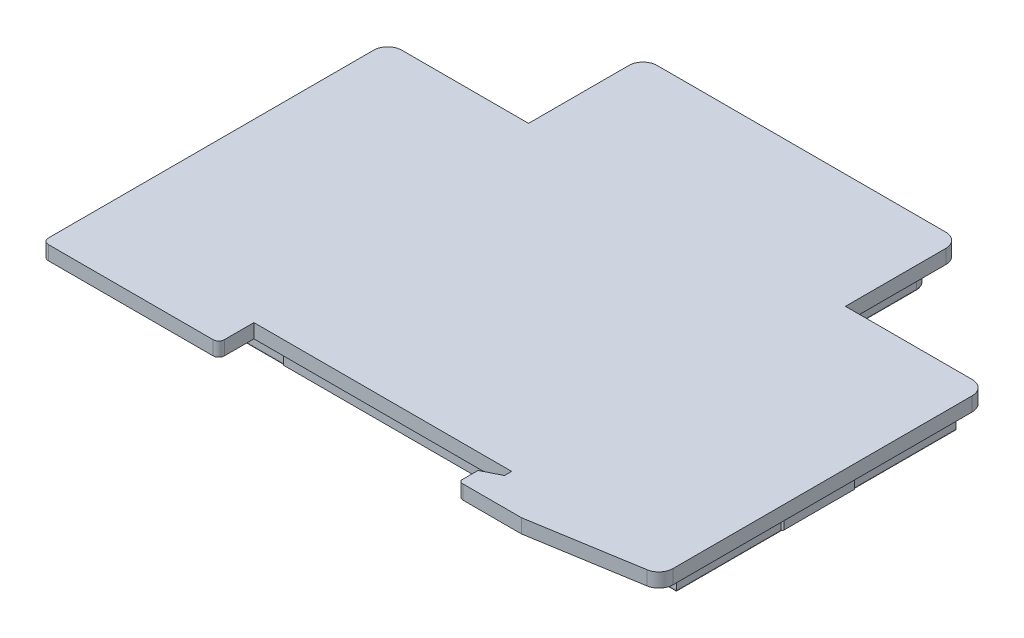
SolidWorks part; units mm, degrees
ref_plane "Front Plane" through (0, 0, 0) normal (0, 0, 1) x (1, 0, 0)
ref_plane "Top Plane" through (0, 0, 0) normal (0, 1, 0) x (1, 0, 0)
ref_plane "Right Plane" through (0, 0, 0) normal (1, 0, 0) x (0, 0, -1)
sketch "Sketch1" plane through (0, 0, 0) normal (0, 1, 0) x (1, 0, 0)
  line L74 (19.5863, 59.9772) -> (19.5863, 47.7272)
  line L75 (58.4363, 61.8272) -> (21.4363, 61.8272)
  line L76 (60.2863, 47.7272) -> (60.2863, 59.9772)
  line L77 (80.2863, 45.5772) -> (62.4363, 45.5772)
  line L78 (80.2863, 5.8772) -> (80.2863, 45.5772)
  line L79 (-0.4137, 5.8772) -> (80.2863, 5.8772)
  line L80 (-0.4137, 45.5772) -> (-0.4137, 5.8772)
  line L81 (17.4363, 45.5772) -> (-0.4137, 45.5772)
  line L82 (19.5863, 59.9772) -> (19.5863, 47.7272)
  line L83 (58.4363, 61.8272) -> (21.4363, 61.8272)
  line L84 (60.2863, 47.7272) -> (60.2863, 59.9772)
  line L85 (80.2863, 45.5772) -> (62.4363, 45.5772)
  line L86 (80.2863, 5.8772) -> (80.2863, 45.5772)
  line L87 (-0.4137, 5.8772) -> (80.2863, 5.8772)
  line L88 (-0.4137, 45.5772) -> (-0.4137, 5.8772)
  line L89 (17.4363, 45.5772) -> (-0.4137, 45.5772)
  arc A20 (17.4363, 45.5772) -> (19.5863, 47.7272) centre (17.4363, 47.7272) ccw
  arc A21 (21.4363, 61.8272) -> (19.5863, 59.9772) centre (21.4363, 59.9772) ccw
  arc A22 (60.2863, 59.9772) -> (58.4363, 61.8272) centre (58.4363, 59.9772) ccw
  arc A23 (60.2863, 47.7272) -> (62.4363, 45.5772) centre (62.4363, 47.7272) ccw
  arc A24 (17.4363, 45.5772) -> (19.5863, 47.7272) centre (17.4363, 47.7272) ccw
  arc A25 (21.4363, 61.8272) -> (19.5863, 59.9772) centre (21.4363, 59.9772) ccw
  arc A26 (60.2863, 59.9772) -> (58.4363, 61.8272) centre (58.4363, 59.9772) ccw
  arc A27 (60.2863, 47.7272) -> (62.4363, 45.5772) centre (62.4363, 47.7272) ccw
  dimension "D1" = 0.15
extrude "Boss-Extrude1" add sketch "Sketch1" along normal blind 3.3
sketch "Sketch2" plane through (0, 3.3, 0) normal (0, 1, 0) x (1, 0, 0)
  line L15 (56.3363, 1.5772) -> (56.3363, -0.4728)
  line L16 (57.1363, -1.2728) -> (65.4363, -1.2728)
  line L17 (65.4363, -1.2728) -> (80.7613, 1.2513)
  line L18 (82.4363, 3.2247) -> (82.4363, 45.7272)
  line L19 (80.4363, 47.7272) -> (76.4363, 47.7272)
  line L20 (62.4363, 47.7272) -> (62.4363, 61.9772)
  line L21 (60.4363, 63.9772) -> (19.4363, 63.9772)
  line L22 (17.4363, 61.9772) -> (17.4363, 47.7272)
  line L23 (17.4363, 47.7272) -> (13.4363, 47.7272)
  line L24 (-2.5637, 45.7272) -> (-2.5637, -0.4728)
  line L25 (-1.7637, -1.2728) -> (21.6363, -1.2728)
  line L26 (22.4363, -0.4728) -> (22.4363, 3.7272)
  line L27 (22.4363, 3.7272) -> (58.8363, 3.7272)
  line L28 (58.8363, 3.7272) -> (58.8363, 2.8272)
  line L29 (58.8363, 2.8272) -> (56.3363, 1.5772)
  line L30 (56.3363, 1.5772) -> (56.3363, -0.4728) construction
  line L31 (57.1363, -1.2728) -> (65.4363, -1.2728)
  line L32 (65.4363, -1.2728) -> (80.7613, 1.2513)
  line L33 (82.4363, 3.2247) -> (82.4363, 45.7272)
  line L34 (80.4363, 47.7272) -> (66.4363, 47.7272)
  line L35 (62.4363, 47.7272) -> (62.4363, 61.9772)
  line L36 (60.4363, 63.9772) -> (19.4363, 63.9772)
  line L37 (17.4363, 61.9772) -> (17.4363, 47.7272)
  line L38 (17.4363, 47.7272) -> (3.4363, 47.7272)
  line L39 (-2.5637, 45.7272) -> (-2.5637, -0.4728)
  line L40 (-1.7637, -1.2728) -> (21.6363, -1.2728)
  line L41 (22.4363, -0.4728) -> (22.4363, 3.7272)
  line L42 (22.4363, 3.7272) -> (59.0363, 3.7272)
  line L43 (58.8363, 3.7272) -> (58.8363, 2.8272) construction
  line L44 (58.8363, 2.8272) -> (56.3363, 1.5772) construction
  line L90 (59.0363, 3.7272) -> (59.0363, 2.7036)
  line L91 (59.0363, 2.7036) -> (56.5363, 1.4536)
  line L92 (56.5363, 1.4536) -> (56.5363, -1.002)
  line L93 (56.5363, 1.4536) -> (56.5363, -0.4728) construction
  line L170 (76.4363, 47.4272) -> (66.4363, 47.4272)
  line L171 (76.4363, 47.4272) -> (66.4363, 47.4272) construction
  line L172 (66.4363, 47.4272) -> (66.4363, 47.7272)
  line L173 (66.4363, 47.4272) -> (66.4363, 47.7272) construction
  line L174 (66.4363, 47.7272) -> (62.4363, 47.7272)
  line L175 (66.4363, 47.7272) -> (62.4363, 47.7272)
  line L176 (13.4363, 47.7272) -> (13.4363, 47.4272)
  line L177 (13.4363, 47.7272) -> (13.4363, 47.4272) construction
  line L178 (13.4363, 47.4272) -> (3.4363, 47.4272)
  line L179 (13.4363, 47.4272) -> (3.4363, 47.4272) construction
  line L180 (3.4363, 47.4272) -> (3.4363, 47.7272)
  line L181 (3.4363, 47.4272) -> (3.4363, 47.7272) construction
  line L182 (3.4363, 47.7272) -> (-0.5637, 47.7272)
  line L183 (3.4363, 47.7272) -> (-0.5637, 47.7272)
  line L184 (76.4363, 47.7272) -> (76.4363, 47.4272)
  line L185 (76.4363, 47.7272) -> (76.4363, 47.4272) construction
  arc A8 (56.3363, -0.4728) -> (57.1363, -1.2728) centre (57.1363, -0.4728) ccw
  arc A9 (80.7613, 1.2513) -> (82.4363, 3.2247) centre (80.4363, 3.2247) ccw
  arc A10 (82.4363, 45.7272) -> (80.4363, 47.7272) centre (80.4363, 45.7272) ccw
  arc A11 (62.4363, 61.9772) -> (60.4363, 63.9772) centre (60.4363, 61.9772) ccw
  arc A12 (19.4363, 63.9772) -> (17.4363, 61.9772) centre (19.4363, 61.9772) ccw
  arc A13 (-0.5637, 47.7272) -> (-2.5637, 45.7272) centre (-0.5637, 45.7272) ccw
  arc A14 (-2.5637, -0.4728) -> (-1.7637, -1.2728) centre (-1.7637, -0.4728) ccw
  arc A15 (21.6363, -1.2728) -> (22.4363, -0.4728) centre (21.6363, -0.4728) ccw
  arc A16 (56.5363, -1.002) -> (57.1363, -1.2728) centre (57.1363, -0.4728) ccw
  arc A17 (80.7613, 1.2513) -> (82.4363, 3.2247) centre (80.4363, 3.2247) ccw
  arc A18 (82.4363, 45.7272) -> (80.4363, 47.7272) centre (80.4363, 45.7272) ccw
  arc A19 (62.4363, 61.9772) -> (60.4363, 63.9772) centre (60.4363, 61.9772) ccw
  arc A20 (19.4363, 63.9772) -> (17.4363, 61.9772) centre (19.4363, 61.9772) ccw
  arc A21 (-0.5637, 47.7272) -> (-2.5637, 45.7272) centre (-0.5637, 45.7272) ccw
  arc A22 (-2.5637, -0.4728) -> (-1.7637, -1.2728) centre (-1.7637, -0.4728) ccw
  arc A23 (21.6363, -1.2728) -> (22.4363, -0.4728) centre (21.6363, -0.4728) ccw
  arc A48 (56.3363, -0.4728) -> (56.5363, -1.002) centre (57.1363, -0.4728) ccw construction
  arc A49 (56.5363, -0.4728) -> (57.1363, -1.0728) centre (57.1363, -0.4728) ccw construction
  arc A50 (56.3363, -0.4728) -> (57.1363, -1.2728) centre (57.1363, -0.4728) ccw construction
  dimension "D1" = 0
  dimension "D2" = 0.2
extrude "Boss-Extrude2" add sketch "Sketch2" along normal blind 2
sketch "Sketch5" plane through (0, 0, -45.5772) normal (0, 0, -1) x (-1, 0, 0)
  line L0 (-80.2863, 3.3) -> (-62.4363, 3.3) construction
  line L1 (-76.4363, 1.8) -> (-66.4363, 1.8)
  line L2 (-76.4363, 1.8) -> (-76.4363, 0.25)
  line L3 (-76.4363, 0.25) -> (-66.4363, 0.25)
  line L4 (-66.4363, 1.8) -> (-66.4363, 0.25)
  line L5 (-80.2863, 0) -> (0.4137, 0) construction
  line L6 (-3.4363, 0.25) -> (-13.4363, 0.25)
  line L7 (-39.9363, -8.663) -> (-39.9363, 0) construction
  line L8 (-13.4363, 1.8) -> (-13.4363, 0.25)
  line L9 (-3.4363, 1.8) -> (-13.4363, 1.8)
  line L10 (-3.4363, 1.8) -> (-3.4363, 0.25)
  line L11 (-76.4363, 1.3) -> (-66.4363, 1.3) construction
  point P16 (-71.4363, 1.8)
  point P19 (-71.4363, 1.3)
  dimension "D1" = 10
  dimension "D2" = 1.5
  dimension "D3" = 1.55
extrude "Boss-Extrude3" add sketch "Sketch5" along normal blind 0.45
sketch "Sketch6" plane through (0, 0, -61.8272) normal (0, 0, -1) x (-1, 0, 0)
  line L1 (-44.9363, 1.8) -> (-34.9363, 1.8)
  line L2 (-44.9363, 1.8) -> (-44.9363, 0.25)
  line L3 (-44.9363, 0.25) -> (-34.9363, 0.25)
  line L4 (-34.9363, 1.8) -> (-34.9363, 0.25)
  line L5 (-58.4363, 0) -> (-21.4363, 0) construction
  line L7 (-58.4363, 3.3) -> (-21.4363, 3.3) construction
  point P6 (-39.9363, 0)
  point P16 (-39.9363, 1.8)
  dimension "D1" = 10
  dimension "D2" = 1.5
  dimension "D3" = 1.55
extrude "Boss-Extrude4" add sketch "Sketch6" along normal blind 0.45
sketch "Sketch7" plane through (-0.4137, 0, 0.3637) normal (-1, 0, 0) x (0, 0, 1)
  line L0 (-45.9409, 0) -> (-6.2409, 0) construction
  line L1 (-31.0909, 1.8) -> (-21.0909, 1.8)
  line L2 (-31.0909, 1.8) -> (-31.0909, 0.25)
  line L3 (-31.0909, 0.25) -> (-21.0909, 0.25)
  line L4 (-21.0909, 1.8) -> (-21.0909, 0.25)
  line L8 (-45.9409, 3.3) -> (-6.2409, 3.3) construction
  point P6 (-26.0909, 0)
  point P7 (-26.0909, 0.25)
  dimension "D1" = 10
  dimension "D2" = 1.5
  dimension "D3" = 1.55
extrude "Boss-Extrude5" add sketch "Sketch7" along normal blind 0.45
sketch "Sketch8" plane through (80.2863, 0, -80.2363) normal (-1, 0, 0) x (0, 0, 1)
  line L0 (74.3591, 0) -> (34.6591, 0) construction
  line L1 (49.5091, 1.8) -> (59.5091, 1.8)
  line L2 (49.5091, 1.8) -> (49.5091, 0.25)
  line L3 (49.5091, 0.25) -> (59.5091, 0.25)
  line L4 (59.5091, 1.8) -> (59.5091, 0.25)
  line L8 (74.3591, 3.3) -> (34.6591, 3.3) construction
  point P6 (54.5091, 0)
  point P16 (54.5091, 1.8)
  dimension "D1" = 10
  dimension "D2" = 1.5
  dimension "D3" = 1.55
extrude "Boss-Extrude6" add sketch "Sketch8" along normal blind 0.45
sketch "Sketch9" plane through (0, 0, -5.8772) normal (0, 0, 1) x (1, 0, 0)
  line L0 (-0.4137, 0) -> (80.2863, 0) construction
  line L1 (24.9363, 1.8) -> (54.9363, 1.8)
  line L2 (24.9363, 1.8) -> (24.9363, 0.25)
  line L3 (24.9363, 0.25) -> (54.9363, 0.25)
  line L4 (54.9363, 1.8) -> (54.9363, 0.25)
  line L8 (-0.4137, 3.3) -> (80.2863, 3.3) construction
  point P4 (39.9363, 0.25)
  point P7 (39.9363, 0)
  dimension "D1" = 30
  dimension "D2" = 1.5
  dimension "D3" = 1.55
extrude "Boss-Extrude7" add sketch "Sketch9" along normal blind 0.45 contours L1 L4 L3 L2
sketch "Sketch10" plane through (80.2863, 0, 0) normal (1, 0, 0) x (0, 0, -1)
  line L0 (5.8772, 0) -> (45.5772, 0) construction
  line L1 (20.7272, 1.8) -> (30.7272, 1.8)
  line L2 (20.7272, 1.8) -> (20.7272, 0.25)
  line L3 (20.7272, 0.25) -> (30.7272, 0.25)
  line L4 (30.7272, 1.8) -> (30.7272, 0.25)
  line L8 (5.8772, 3.3) -> (45.5772, 3.3) construction
  point P4 (25.7272, 0.25)
  point P7 (25.7272, 0)
  dimension "D1" = 10
  dimension "D2" = 1.5
  dimension "D3" = 1.55
extrude "Boss-Extrude8" add sketch "Sketch10" along normal blind 0.45
chamfer "Chamfer1" distance 0.2 angle 45 12 edges at (-0.8637, 0.25, -25.7272) (-0.8637, 1.8, -25.7272) (39.9363, 1.8, -5.4272) (39.9363, 0.25, -5.4272) (80.7363, 0.25, -25.7272) (80.7363, 1.8, -25.7272) (71.4363, 0.25, -46.0272) (71.4363, 1.8, -46.0272) (8.4363, 1.8, -46.0272) (8.4363, 0.25, -46.0272) (39.9363, 0.25, -62.2772) (39.9363, 1.8, -62.2772)
sketch "Sketch11" plane through (0, 0, 0) normal (0, -1, 0) x (-1, 0, 0)
  line L0 (-46.3963, 38.3972) -> (-43.2763, 38.3972) construction
  line L1 (-12.1963, 18.3972) -> (-46.3963, 18.3972) construction
  line L2 (-12.1963, 18.3972) -> (-12.1963, 38.3972) construction
  line L3 (-12.1963, 38.3972) -> (-46.3963, 38.3972) construction
  line L4 (-46.3963, 18.3972) -> (-46.3963, 38.3972) construction
  line L5 (-12.1963, 18.3972) -> (-46.3963, 18.3972) construction
  line L6 (-12.1963, 38.3972) -> (-12.1963, 18.3972) construction
  line L7 (-46.3963, 18.3972) -> (-46.3963, 38.3972) construction
  line L8 (-10.6963, 16.8972) -> (-10.6963, 39.8972)
  line L9 (-10.6963, 39.8972) -> (-47.8963, 39.8972)
  line L10 (-47.8963, 16.8972) -> (-47.8963, 39.8972)
  line L11 (-10.6963, 16.8972) -> (-47.8963, 16.8972)
  dimension "D1" = 1.5
extrude "Cut-Extrude1" cut sketch "Sketch11" against normal blind 1.6
fillet "Fillet1" radius 0.2 16 edges at (8.5113, 0, -45.5772) (-0.4137, 0, -25.7272) (39.9363, 0, -5.8772) (80.2863, 0, -25.7272) (71.3613, 0, -45.5772) (60.916, 0, -46.2069) (60.2863, 0, -53.8522) (59.7444, 0, -61.2853) (39.9363, 0, -61.8272) (20.1281, 0, -61.2853) (19.5863, 0, -53.8522) (18.9566, 0, -46.2069) (29.2963, 0, -39.8972) (47.8963, 0, -28.3972) (29.2963, 0, -16.8972) (10.6963, 0, -28.3972)
